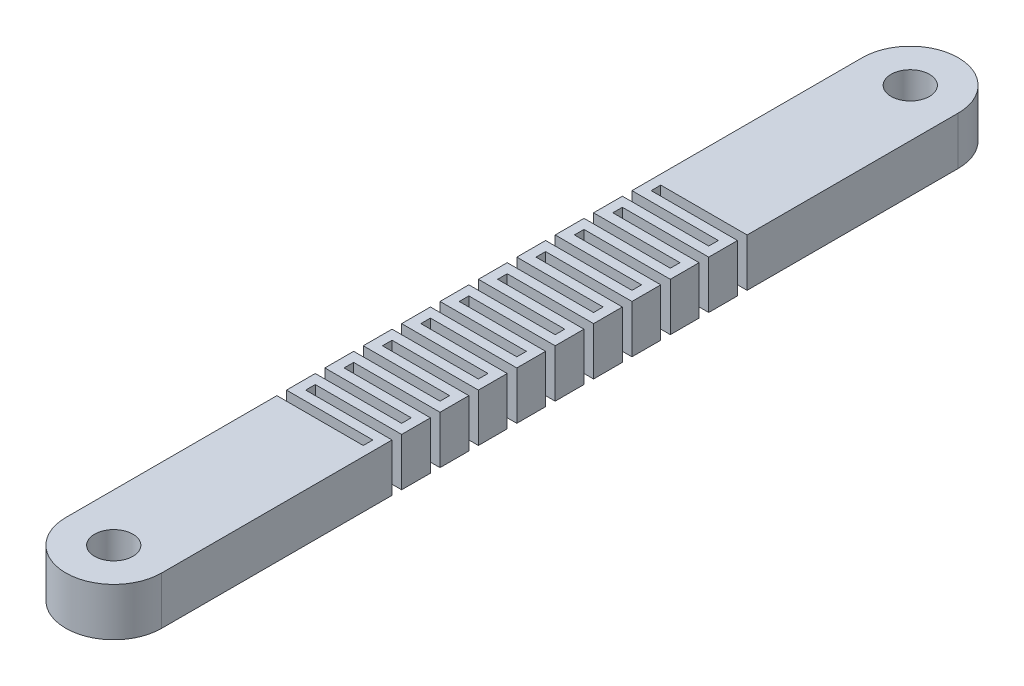
SolidWorks part; units mm, degrees
ref_plane "Front Plane" through (0, 0, 0) normal (0, 0, 1) x (1, 0, 0)
ref_plane "Top Plane" through (0, 0, 0) normal (0, 1, 0) x (1, 0, 0)
ref_plane "Right Plane" through (0, 0, 0) normal (1, 0, 0) x (0, 0, -1)
sketch "Sketch1" plane through (0, 0, 0) normal (0, 1, 0) x (1, 0, 0)
  line L0 (0, 41.5) -> (0, -41.5) construction
  line L1 (5, 41.5) -> (5, -41.5)
  line L2 (-5, 41.5) -> (-5, -41.5)
  arc A0 (5, 41.5) -> (-5, 41.5) centre (0, 41.5) ccw
  arc A1 (-5, -41.5) -> (5, -41.5) centre (0, -41.5) ccw
  circle A2 centre (0, 41.5) radius 2
  circle A3 centre (0, -41.5) radius 2
  point P2 (0, 0)
  dimension "D1" = 83
  dimension "D2" = 10
extrude "Boss-Extrude1" add sketch "Sketch1" along normal blind 5
sketch "Sketch2" plane through (0, 5, 0) normal (0, 1, 0) x (1, 0, 0)
  line L0 (5, -41.5) -> (5, 41.5) construction
  line L1 (14, 2.5) -> (-4, 2.5)
  line L2 (14, 2.5) -> (14, 3.5)
  line L3 (14, 3.5) -> (-4, 3.5)
  line L4 (-4, 2.5) -> (-4, 3.5)
  line L5 (14, 2.5) -> (-4, 3.5) construction
  line L6 (14, 3.5) -> (-4, 2.5) construction
  line L7 (-5, 41.5) -> (-5, -41.5) construction
  line L8 (-14, 1.5) -> (4, 1.5)
  line L9 (-14, 1.5) -> (-14, 0.5)
  line L10 (-14, 0.5) -> (4, 0.5)
  line L11 (4, 1.5) -> (4, 0.5)
  line L12 (-14, 1.5) -> (4, 0.5) construction
  line L13 (-14, 0.5) -> (4, 1.5) construction
  point P0 (5, 3)
  point P7 (-5, 1)
  dimension "D1" = 0.5
  dimension "D2" = 1
  dimension "D3" = 1
  dimension "D4" = 1
  dimension "D5" = 1
  dimension "D6" = 1
extrude "Cut-Extrude1" cut sketch "Sketch2" against normal through all
pattern_linear "LPattern1" count 5 spacing 4 along (0, 0, -1) count 6 spacing 4 along (0, 0, 1) of "Cut-Extrude1"
